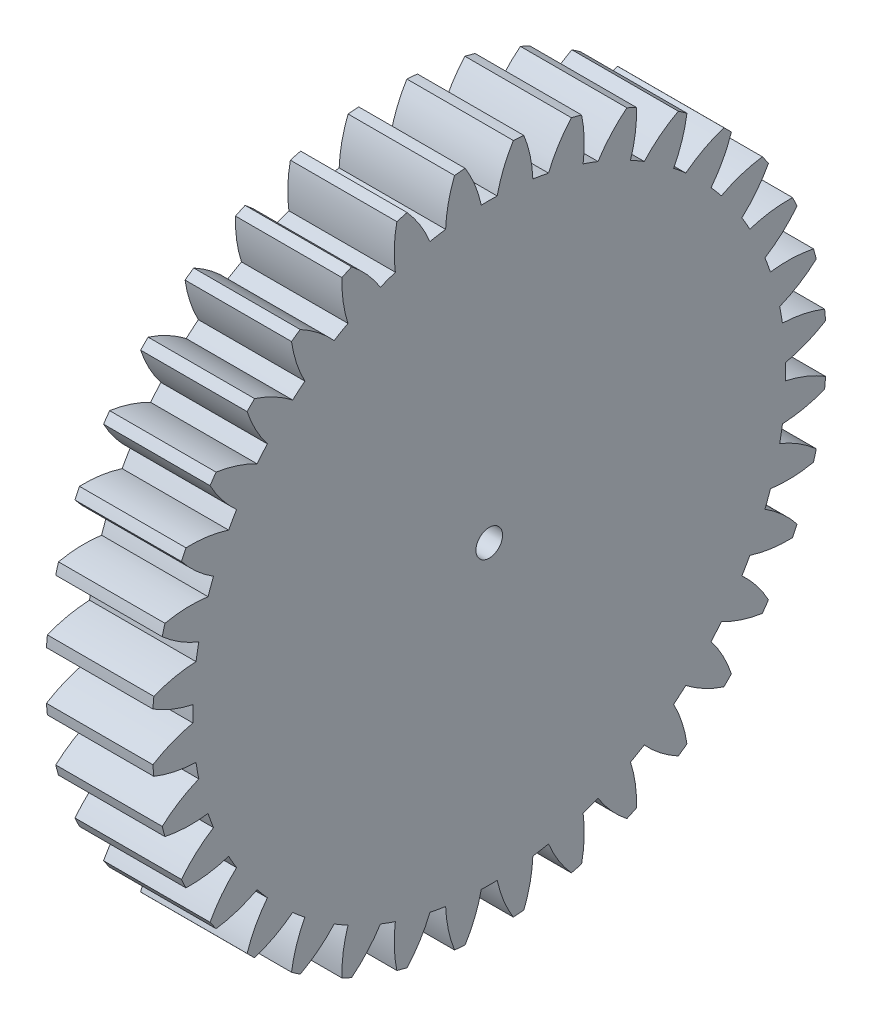
SolidWorks part; units mm, degrees
material "PET"
ref_plane "Plane1" through (0, 0, 0) normal (0, 0, 1) x (1, 0, 0)
ref_plane "Plane2" through (0, 0, 0) normal (0, 1, 0) x (1, 0, 0)
ref_plane "Plane3" through (0, 0, 0) normal (1, 0, 0) x (0, 0, -1)
sketch "HoldingSke" plane through (0, 0, 0) normal (0, 1, 0) x (1, 0, 0)
  line L0 (0, 0) -> (986.3535, -716.6278)
  line L1 (-15, 0) -> (100, 0) construction
  line L2 (0, 0) -> (-2.1039, 2.3779)
  line L3 (0, 0) -> (-11.863, 4.5341)
  line L4 (0, 0) -> (6.9867, 5.0761)
  line L5 (0, 0) -> (-47.5972, -17.7524)
  line L6 (0, 0) -> (-2.632, -1.7758)
  line L7 (-2.1039, 2.3779) -> (8.8308, 51.9871)
  line L8 (-76.2, 54.61) -> (-75.184, 54.61)
  line L9 (-71.009, 38.7566) -> (-53.1078, 45.2721)
  line L10 (-76.2, 71.12) -> (104.1128, 71.12)
  line L11 (0, 0) -> (-3.175, 0)
  line L12 (-76.2, 101.6) -> (-76.1787, 101.6)
  line L13 (24.9733, 27.94) -> (52.9518, 28.4284)
  line L14 (24.9733, 27.94) -> (25.0241, 27.9398)
  line L15 (24.9733, 27.94) -> (100.4021, 29.52)
  circle A0 centre (0, 0) radius 0.3969
  circle A1 centre (0, 0) radius 8.8392
  circle A2 centre (0, 0) radius 38.1
  circle A3 centre (0, 0) radius 0.3969
  dimension "MHD" = 17.6784
  dimension "Hub_dia" = 76.2
  dimension "Bore" = 0.7937
  dimension "MBD" = 0.7937
  dimension "Num_teeth" = 36
  dimension "Pitch" = 1219.2
  dimension "Overall_len" = 50.8
  dimension "Show_teeth" = 36
  dimension "Thickness" = 3.175
  dimension "OAL" = 50.8001
  dimension "T_dim" = 1.016
  dimension "Ap" = 20
  dimension "H" = 19.05
  dimension "Pitch_radius" = 180.3128
  dimension "Width" = 3.175
  dimension "Backlash" = 0.0213
  dimension "Addendum_fac" = 1
  dimension "Dedendum_fac" = 1.2
  dimension "Clearance_fac" = 0.2
  dimension "Dedendum_add" = 0.0508
sketch "BasProSke" plane through (0, 0, 0) normal (0, 1, 0) x (1, 0, 0)
  line L0 (-10, 0) -> (60, 0) construction
  line L1 (0, 0) -> (0, 10.0542)
  line L2 (0, 0) -> (3.175, 0)
  line L3 (3.175, 0) -> (3.175, 10.0542)
  line L4 (3.175, 10.0542) -> (0, 10.0542)
  dimension "Thickness" = 3.175
  dimension "Diameter" = 20.1083
revolve "Base-Revolve" add sketch "BasProSke" angle 360 about L0
sketch "TooCutSke" plane through (0, 0, 0) normal (1, 0, 0) x (0, 0, -1)
  line L1 (0, 0) -> (0, 107) construction
  line L2 (0, 0) -> (-0.4528, 9.5142) construction
  line L3 (0, 0) -> (-1.659, 18.9625) construction
  line L4 (-0.4528, 9.5142) -> (-0.8295, 9.4813) construction
  arc A0 (0.2374, 8.836) -> (-0.2374, 8.836) centre (0, 0) ccw
  arc A1 (0.7338, 10.0528) -> (-0.7338, 10.0528) centre (0, 0) ccw
  circle A2 centre (0, 0) radius 9.525 construction
  circle A3 centre (0, 0) radius 8.9506 construction
  arc A4 (-0.2374, 8.836) -> (-0.7338, 10.0528) centre (-3.9604, 8.0267) ccw
  arc A5 (0.7338, 10.0528) -> (0.2374, 8.836) centre (3.9604, 8.0267) ccw
  dimension "Root_dia" = 17.6784
  dimension "Overcut_dia" = 20.1591
  dimension "Pitch_dia" = 19.05
  dimension "Base_dia" = 17.9011
  dimension "Flank_rad" = 3.81
  dimension "Half_ang" = 5
  dimension "Half_CT" = 0.3781
extrude "ToothCut" cut sketch "TooCutSke" along normal through all
fillet "Breaks" [suppressed] radius 0.0106
fillet "RootFillets" [suppressed] radius 0.1566
pattern_circular "TeethCuts" count 36 every 10 about axis through (-10, 0, 0) along (1, 0, 0) of "ToothCut", "RootFillets", "Breaks"
sketch "HubNeaOneSke" plane through (0, 0, 0) normal (-1, 0, 0) x (0, 0, 1)
  circle A0 centre (0, 0) radius 8.8392
  dimension "Diameter" = 17.6784
extrude "HubNearOne" [suppressed] add sketch "HubNeaOneSke" along normal blind 47.6251
sketch "HubNeaBotSke" plane through (0, 0, 0) normal (-1, 0, 0) x (0, 0, 1)
  circle A0 centre (0, 0) radius 8.8392
  dimension "Diameter" = 17.6784
extrude "HubNearBoth" [suppressed] add sketch "HubNeaBotSke" along normal blind 23.8125
ref_plane "FarPln" through (3.175, 0, 0) normal (1, 0, 0) x (0, 0, -1)
sketch "HubFarSke" plane through (3.175, 0, 0) normal (1, 0, 0) x (0, 0, -1)
  circle A0 centre (0, 0) radius 8.8392
  dimension "Diameter" = 17.6784
extrude "HubFar" [suppressed] add sketch "HubFarSke" along normal blind 23.8125
sketch "BorSke" plane through (0, 0, 0) normal (1, 0, 0) x (0, 0, -1)
  circle A0 centre (0, 0) radius 0.3969
  dimension "Diameter" = 0.7937
extrude "Bore" cut sketch "BorSke" along normal mid plane 101.6001
sketch "KeySke" plane through (0, 0, 0) normal (1, 0, 0) x (0, 0, -1)
  line L0 (-0.127, 0) -> (-0.127, 0.6191)
  line L1 (-0.127, 0.6191) -> (0.127, 0.6191)
  line L2 (0.127, 0.6191) -> (0.127, 0)
  line L3 (0, 0) -> (0, 34) construction
  line L4 (-0.127, 0) -> (0.127, 0)
  dimension "Offset" = 0.6191
  dimension "Width" = 0.254
extrude "Keyway" [suppressed] cut sketch "KeySke" along normal mid plane 101.6001
pattern_circular "Keyway2" [suppressed] count 2 every 90 about axis through (-10, 0, 0) along (1, 0, 0)
sketch "Sketch1" plane through (3.175, 0, 0) normal (1, 0, 0) x (0, 0, -1)
  circle A0 centre (0, 0) radius 1.5875
  dimension "D1" = 3.175
extrude "Boss-Extrude1" [suppressed] add sketch "Sketch1" along normal blind 25.4
chamfer "Chamfer1" [suppressed] distance 0.3 angle 45
ref_plane "Plane4" through (1.5875, 0, 0) normal (-1, 0, 0) x (0, 0, 1)
sketch "Sketch5" plane through (1.5875, 0, 0) normal (-1, 0, 0) x (0, 0, 1)
  arc A0 (0.7186, 10.0285) -> (0.2374, 8.836) centre (3.9604, 8.0267) ccw construction
  circle A1 centre (0, 0) radius 9.4623
  point P0 (0.4273, 9.4527)
sketch "Sketch7" plane through (0, 0, 0) normal (-1, 0, 0) x (0, 0, 1)
  circle A0 centre (0, 0) radius 2.7781
  dimension "D1" = 5.5562
extrude "Cut-Extrude2" cut sketch "Sketch7" against normal offset from surface (1.5875 mm away) 1.5875 up to face at (3.175, 0, 0.3969)
sketch "Sketch8" plane through (0, 0, 0) normal (-1, 0, 0) x (0, 0, 1)
  circle A0 centre (0, 0) radius 3.175
  circle A1 centre (0, 0) radius 0.3969 construction
  circle A2 centre (0, 0) radius 0.3969
  dimension "D1" = 6.35
extrude "Boss-Extrude2" [suppressed] add sketch "Sketch8" along normal blind 3.175
sketch "Sketch9" plane through (3.175, 0, 0) normal (1, 0, 0) x (0, 0, -1)
  circle A0 centre (0, 0) radius 2.3813
  dimension "D1" = 4.7625
extrude "Cut-Extrude3" [suppressed] cut sketch "Sketch9" against normal offset from surface (4.7625 mm away) 1.5875
equation "' \"Pitch@HoldingSke\" = 4"
equation "' \"Num_teeth@HoldingSke\" = 12"
equation "' \"Ap@HoldingSke\" =  20"
equation "' \"Ap@HoldingSke\" = 20"
equation "' \"Width@HoldingSke\" = 0.5"
equation "' \"Hub_dia@HoldingSke\"= 1"
equation "' \"Hub_dia@HoldingSke\" = 1"
equation "' \"Overall_len@HoldingSke\" = 1.0"
equation "' \"Bore@HoldingSke\" = 0.75"
equation "' \"T_dim@HoldingSke\" = 0.85"
equation "' \"Width@KeySke\" = 0.25"
equation "' \"Show_teeth@HoldingSke\" = 13"
equation "' \"Backlash@HoldingSke\" = 0.009"
equation "' \"Addendum_fac@HoldingSke\" = 1.0"
equation "' \"Dedendum_fac@HoldingSke\" = 1.25"
equation "' \"Dedendum_add@HoldingSke\" = 0.00005"
equation "' \"Clearance_fac@HoldingSke\" = 0.25"
equation "' \"Pitch@HoldingSke\" = 0.5"
equation "' \"Num_teeth@HoldingSke\" = 23"
equation "' \"Show_teeth@HoldingSke\" = 23"
equation "' \"Backlash@HoldingSke\" = 0.0375"
equation "\"Overcut_dia@TooCutSke\" = (\"Num_teeth@HoldingSke\" + 2 * \"Addendum_fac@HoldingSke\") / \"Pitch@HoldingSke\" + 0.002"
equation "\"Pitch_dia@TooCutSke\" = \"Num_teeth@HoldingSke\" / \"Pitch@HoldingSke\""
equation "\"Base_dia@TooCutSke\" = \"Num_teeth@HoldingSke\" / \"Pitch@HoldingSke\" * cos((\"Ap@HoldingSke\"  * 3.14159265 / 180))"
equation "\"Root_dia@TooCutSke\" = (\"Num_teeth@HoldingSke\" + 2) / \"Pitch@HoldingSke\" - 2 * (\"Addendum_fac@HoldingSke\" + \"Dedendum_fac@HoldingSke\") / \"Pitch@HoldingSke\" - \"Dedendum_add@HoldingSke\" * 2"
equation "\"Half_ang@TooCutSke\" = 180 / \"Num_teeth@HoldingSke\""
equation "\"Half_CT@TooCutSke\" = \"Num_teeth@HoldingSke\" / \"Pitch@HoldingSke\" * sin((3.14159265 / 2 / \"Num_teeth@HoldingSke\")) / 2 - 7 * \"Backlash@HoldingSke\" / 4"
equation "\"Flank_rad@TooCutSke\" = \"Num_teeth@HoldingSke\" / \"Pitch@HoldingSke\" / 5"
equation "\"Radius@RootFillets\" = \"Clearance_fac@HoldingSke\" / \"Pitch@HoldingSke\" + \"Dedendum_add@HoldingSke\""
equation "\"Break_rad@Breaks\" = 0.02 / \"Pitch@HoldingSke\""
equation "\"Thickness@HoldingSke\" = \"Width@HoldingSke\""
equation "\"OAL@HoldingSke\" = \"Thickness@HoldingSke\""
equation "\"MHD@HoldingSke\" = (\"Num_teeth@HoldingSke\" + 2) / \"Pitch@HoldingSke\" - 2 * (\"Addendum_fac@HoldingSke\" + \"Dedendum_fac@HoldingSke\")  / \"Pitch@HoldingSke\" - \"Dedendum_add@HoldingSke\" * 2"
equation "\"MBD@HoldingSke\" = (\"Num_teeth@HoldingSke\" + 2) / \"Pitch@HoldingSke\" - 2 * (\"Addendum_fac@HoldingSke\" + \"Dedendum_fac@HoldingSke\")  / \"Pitch@HoldingSke\" - \"Dedendum_add@HoldingSke\" * 2 - 0.002"
equation "\"MHD@HoldingSke\" = ((sgn( \"MHD@HoldingSke\" - \"Hub_dia@HoldingSke\" )-1)*( \"MHD@HoldingSke\" - \"Hub_dia@HoldingSke\" ))/-2+ \"Hub_dia@HoldingSke\""
equation "\"MBD@HoldingSke\" = ((sgn( \"MBD@HoldingSke\" - \"Bore@HoldingSke\" )-1)*( \"MBD@HoldingSke\" - \"Bore@HoldingSke\" ))/-2+ \"Bore@HoldingSke\""
equation "\"OAL@HoldingSke\" = ((sgn( \"OAL@HoldingSke\" - \"Overall_len@HoldingSke\" )+1)*( \"OAL@HoldingSke\" - \"Overall_len@HoldingSke\" ))/2 + \"Overall_len@HoldingSke\" + 0.000002"
equation "\"Num_teeth@TeethCuts\" = int( \"Show_teeth@HoldingSke\" ) + 1"
equation "\"Num_teeth@TeethCuts\" = ((sgn( \"Num_teeth@TeethCuts\" - \"Num_teeth@HoldingSke\" )-1)*( \"Num_teeth@TeethCuts\" - \"Num_teeth@HoldingSke\" ))/-2+ \"Num_teeth@HoldingSke\""
equation "\"Num_teeth@TeethCuts\" = ((sgn( \"Num_teeth@TeethCuts\" - 2.0)+1)*( \"Num_teeth@TeethCuts\" - 2.0))/2 +2.0"
equation "\"Angle@TeethCuts\" = 360.0 / \"Num_teeth@HoldingSke\""
equation "\"Diameter@BasProSke\" = (\"Num_teeth@HoldingSke\" + 2 * \"Addendum_fac@HoldingSke\") / \"Pitch@HoldingSke\""
equation "\"Thickness@BasProSke\"  = \"Thickness@HoldingSke\""
equation "' \"Fillet_rad@BasProSke\" =  \"Thickness@HoldingSke\" * 0.05"
equation "' \"Fillet_rad@BasProSke\" = \"Thickness@HoldingSke\" * 0.05"
equation "\"MHD@HoldingSke\" = ((sgn( \"MHD@HoldingSke\" - \"Root_dia@TooCutSke\" )-1)*( \"MHD@HoldingSke\" - \"Root_dia@TooCutSke\" ))/-2+ \"Root_dia@TooCutSke\""
equation "\"Diameter@HubNeaOneSke\" = \"MHD@HoldingSke\""
equation "\"Length@HubNearOne\" = \"OAL@HoldingSke\" - \"Thickness@BasProSke\""
equation "\"Diameter@HubNeaBotSke\" = \"MHD@HoldingSke\""
equation "\"Length@HubNearBoth\" = ( \"OAL@HoldingSke\" - \"Thickness@BasProSke\" ) / 2.0"
equation "\"Thickness@FarPln\" = \"Thickness@BasProSke\""
equation "\"Diameter@HubFarSke\" = \"MHD@HoldingSke\""
equation "\"Length@HubFar\" = ( \"OAL@HoldingSke\" - \"Thickness@BasProSke\" ) / 2.0"
equation "\"Diameter@BorSke\" = \"MBD@HoldingSke\""
equation "\"D1@Bore\" = \"OAL@HoldingSke\" * 2.0"
equation "\"D1@Keyway\" = \"OAL@HoldingSke\" * 2.0"
equation "\"Offset@KeySke\" = \"T_dim@HoldingSke\" - \"MBD@HoldingSke\" / 2.0"
